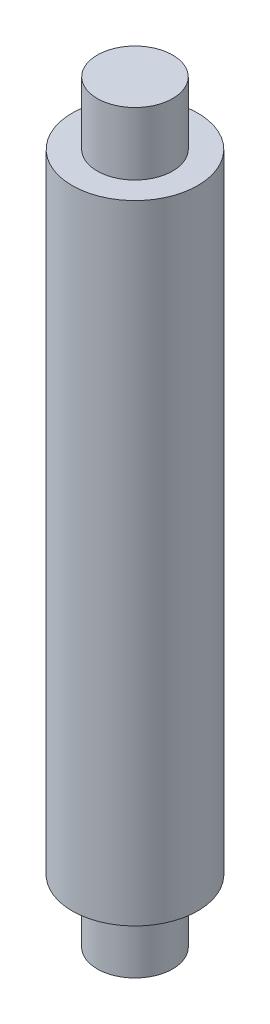
SolidWorks part; units mm, degrees
ref_plane "Alzado" through (0, 0, 0) normal (0, 0, 1) x (1, 0, 0)
ref_plane "Planta" through (0, 0, 0) normal (0, 1, 0) x (1, 0, 0)
ref_plane "Vista lateral" through (0, 0, 0) normal (1, 0, 0) x (0, 0, -1)
sketch "Croquis1" plane through (0, 0, 0) normal (1, 0, 0) x (0, 0, -1)
  line L0 (0, 60) -> (0, -60)
  line L1 (0, -60) -> (-6, -60)
  line L2 (-6, -60) -> (-6, -50)
  line L3 (-6, -50) -> (-10, -50)
  line L4 (-10, -50) -> (-10, 50)
  line L5 (-10, 50) -> (-6, 50)
  line L6 (-6, 50) -> (-6, 60)
  line L7 (-6, 60) -> (0, 60)
  point P4 (0, 0)
  point P6 (0, 0)
  point P13 (-14.8258, -39.8504)
  dimension "D1" = 120
  dimension "D2" = 6
  dimension "D3" = 10
  dimension "D4" = 6
  dimension "D5" = 100
  dimension "D6" = 10
revolve "Revolución1" add sketch "Croquis1" angle 360 about L0
